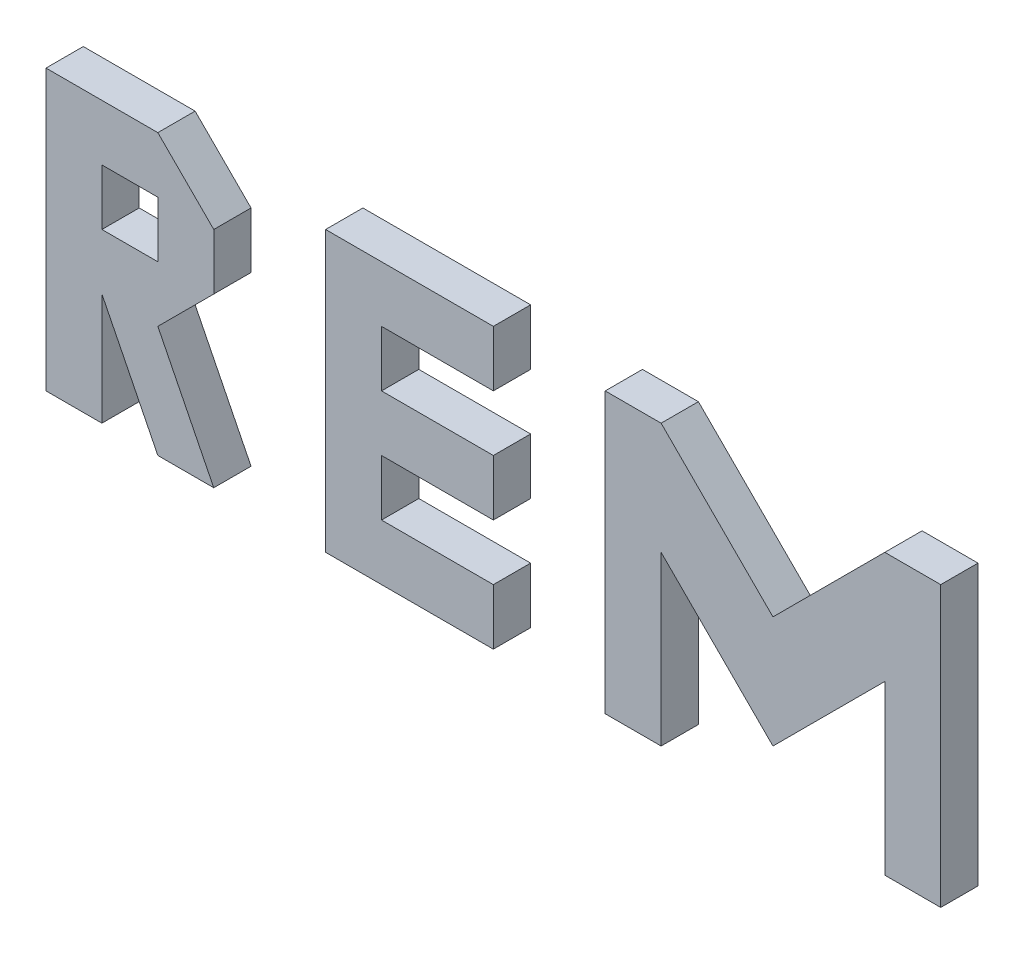
SolidWorks part; units mm, degrees
ref_plane "Front" through (0, 0, 0) normal (0, 0, 1) x (1, 0, 0)
ref_plane "Top" through (0, 0, 0) normal (0, 1, 0) x (1, 0, 0)
ref_plane "Right" through (0, 0, 0) normal (1, 0, 0) x (0, 0, -1)
sketch "Sketch1" plane through (0, 0, 0) normal (0, 0, 1) x (1, 0, 0)
  line L0 (15, 0) -> (15, 30)
  line L1 (0, 0) -> (15, 0)
  line L2 (0, 0) -> (0, 75)
  line L3 (0, 75) -> (30, 75)
  line L4 (240, 0) -> (240, 75)
  line L6 (30, 0) -> (45, 0)
  line L7 (45, 45) -> (45, 60)
  line L8 (75, 0) -> (75, 75)
  line L9 (90, 15) -> (90, 30)
  line L10 (30, 45) -> (30, 60)
  line L11 (120, 0) -> (120, 15)
  line L12 (120, 60) -> (120, 75)
  line L13 (150, 0) -> (150, 75)
  line L14 (165, 0) -> (165, 45)
  line L15 (150, 75) -> (165, 75)
  line L16 (90, 45) -> (90, 60)
  line L17 (15, 45) -> (15, 60)
  line L18 (225, 0) -> (225, 45)
  line L21 (15, 45) -> (30, 45)
  line L22 (15, 60) -> (30, 60)
  line L23 (30, 75) -> (45, 60)
  line L24 (30, 0) -> (15, 30)
  line L25 (45, 0) -> (30, 30)
  line L26 (30, 30) -> (45, 45)
  line L27 (165, 75) -> (195, 45)
  line L28 (195, 45) -> (225, 75)
  line L29 (165, 45) -> (195, 15)
  line L30 (195, 15) -> (225, 45)
  line L31 (225, 0) -> (240, 0)
  line L35 (210, 0) -> (210, 15) [skipped]
  line L38 (180, 0) -> (180, 15) [skipped]
  line L40 (225, 75) -> (240, 75)
  line L44 (150, 0) -> (165, 0)
  line L45 (135, 0) -> (135, 75) [skipped]
  line L47 (120, 30) -> (120, 45)
  line L49 (75, 0) -> (120, 0)
  line L50 (90, 15) -> (120, 15)
  line L51 (90, 30) -> (120, 30)
  line L52 (90, 45) -> (120, 45)
  line L53 (90, 60) -> (120, 60)
  line L54 (75, 75) -> (120, 75)
  line L55 (60, 0) -> (60, 75) [skipped]
  line L56 (45, 0) -> (45, 30) [skipped]
  line L60 (195, 30) -> (195, 45) [skipped]
  line L61 (105, 0) -> (105, 15) [skipped]
  line L62 (0, 15) -> (15, 15) [skipped]
  line L63 (15, 30) -> (30, 30) [skipped]
  line L64 (30, 15) -> (30, 30) [skipped]
extrude "Extrude1" add sketch "Sketch1" along normal blind 10
